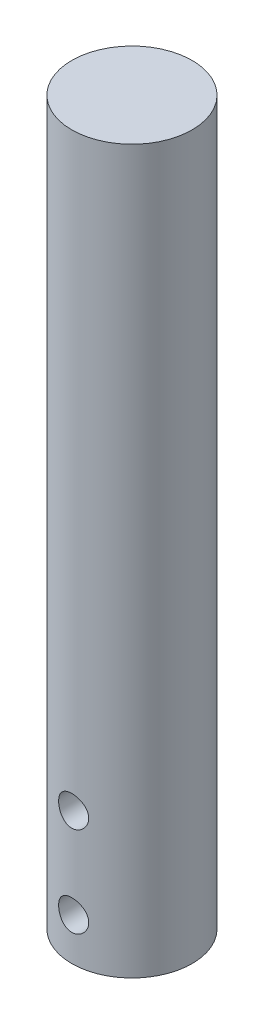
SolidWorks part; units mm, degrees
ref_plane "Front Plane" through (0, 0, 0) normal (0, 0, 1) x (1, 0, 0)
ref_plane "Top Plane" through (0, 0, 0) normal (0, 1, 0) x (1, 0, 0)
ref_plane "Right Plane" through (0, 0, 0) normal (1, 0, 0) x (0, 0, -1)
sketch "Sketch1" plane through (0, 0, 0) normal (0, 1, 0) x (1, 0, 0)
  circle A0 centre (0, 0) radius 12.7
  dimension "D1" = 25.4
extrude "Boss-Extrude1" add sketch "Sketch1" along normal blind 152.4
ref_plane "Plane1" through (0, 0, 12.7) normal (0, 0, 1) x (1, 0, 0)
sketch "Sketch2" plane through (0, 0, 12.7) normal (0, 0, 1) x (1, 0, 0)
  line L0 (0, 0) -> (0, 27.94) construction
  circle A0 centre (0, 27.94) radius 3.175
  circle A1 centre (0, 8.89) radius 3.175
  dimension "D3" = 6.35
  dimension "D1" = 19.05
  dimension "D2" = 8.89
extrude "Cut-Extrude1" cut sketch "Sketch2" against normal through all
